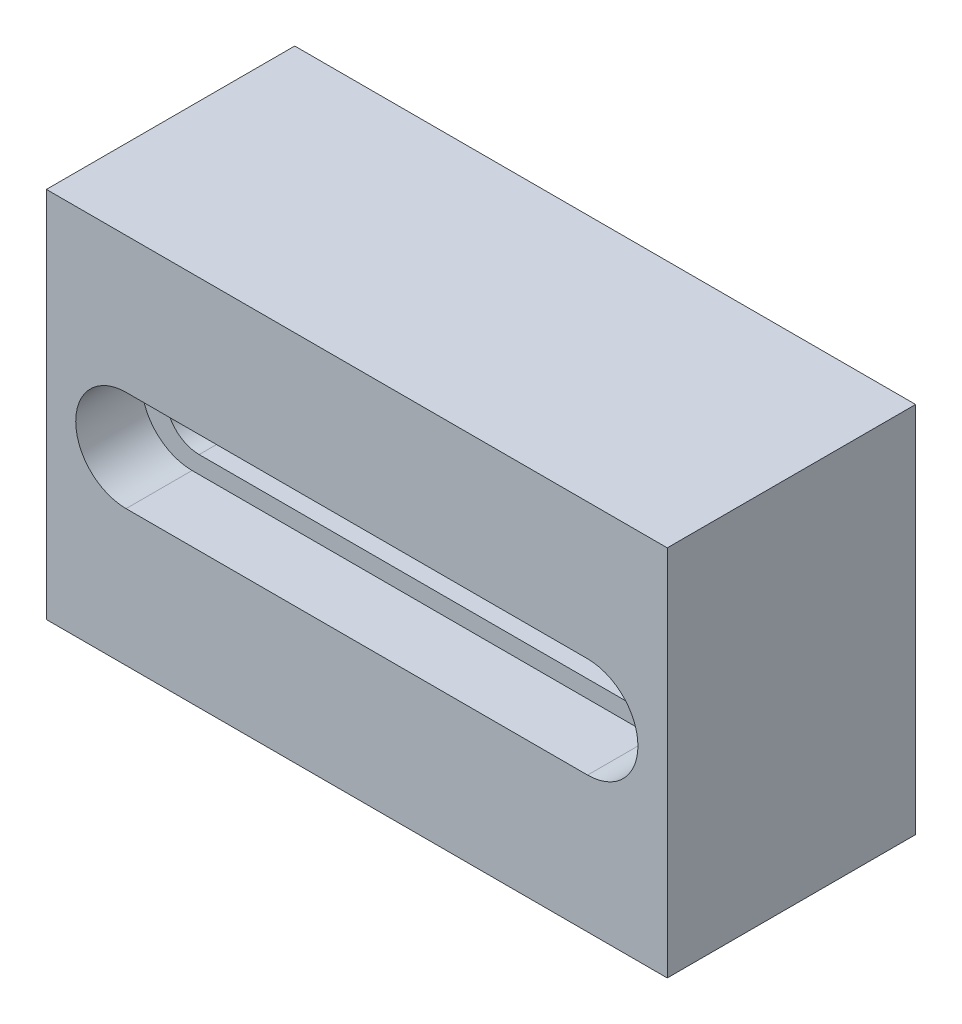
SolidWorks part; units mm, degrees
ref_plane "Front Plane" through (0, 0, 0) normal (0, 0, 1) x (1, 0, 0)
ref_plane "Top Plane" through (0, 0, 0) normal (0, 1, 0) x (1, 0, 0)
ref_plane "Right Plane" through (0, 0, 0) normal (1, 0, 0) x (0, 0, -1)
sketch "Sketch1" plane through (0, 0, 0) normal (0, 1, 0) x (1, 0, 0)
  line L1 (0, 0) -> (127, 0)
  line L2 (0, 0) -> (0, 50.8)
  line L3 (0, 50.8) -> (127, 50.8)
  line L4 (127, 0) -> (127, 50.8)
  dimension "D1" = 50.8
  dimension "D2" = 127
extrude "Boss-Extrude1" add sketch "Sketch1" along normal blind 76.2
sketch "Sketch2" plane through (0, 0, 0) normal (0, 0, 1) x (1, 0, 0)
  line L0 (116, 38.1) -> (11, 38.1) construction
  line L1 (0, 0) -> (63.5, 0)
  line L2 (0, 0) -> (0, 38.1)
  line L3 (0, 38.1) -> (63.5, 38.1)
  line L4 (63.5, 0) -> (63.5, 38.1)
  line L5 (11, 44.85) -> (116, 44.85)
  line L6 (11, 44.85) -> (11, 31.35)
  line L7 (11, 31.35) -> (116, 31.35)
  line L8 (116, 44.85) -> (116, 31.35)
  line L9 (11, 44.85) -> (116, 31.35) construction
  line L10 (11, 31.35) -> (116, 44.85) construction
  circle A0 centre (109.25, 38.1) radius 6.75
  circle A1 centre (17.75, 38.1) radius 6.75
  dimension "D1" = 38.1
  dimension "D2" = 63.5
  dimension "D3" = 105
  dimension "D4" = 13.5
sketch "Sketch3" plane through (0, 0, 0) normal (0, 0, 1) x (1, 0, 0)
  line L1 (0, 0) -> (63.5, 0)
  line L2 (0, 0) -> (0, 38.1)
  line L3 (0, 38.1) -> (63.5, 38.1)
  line L4 (63.5, 0) -> (63.5, 38.1)
  line L5 (6, 48.4) -> (121, 48.4)
  line L6 (6, 48.4) -> (6, 27.8)
  line L7 (6, 27.8) -> (121, 27.8)
  line L8 (121, 48.4) -> (121, 27.8)
  line L9 (6, 48.4) -> (121, 27.8) construction
  line L10 (6, 27.8) -> (121, 48.4) construction
  circle A0 centre (16.3, 38.1) radius 10.3
  circle A2 centre (110.7, 38.1) radius 10.3
  dimension "D4" = 115
  dimension "D1" = 63.5
  dimension "D2" = 38.1
  dimension "D3" = 20.6
extrude "Cut-Extrude5" cut sketch "Sketch2" against normal through all contours A1 L3 L4 L7 A0 L5 | A1 L7 L4 L3 | A0 | L3 A1 | L3 A1
extrude "Cut-Extrude6" cut sketch "Sketch3" against normal blind 13.5 contours A2 L5 A0 L3 L4 L7 | A0 L7 L4 L3 | L3 A0 | L3 A0 | A2
